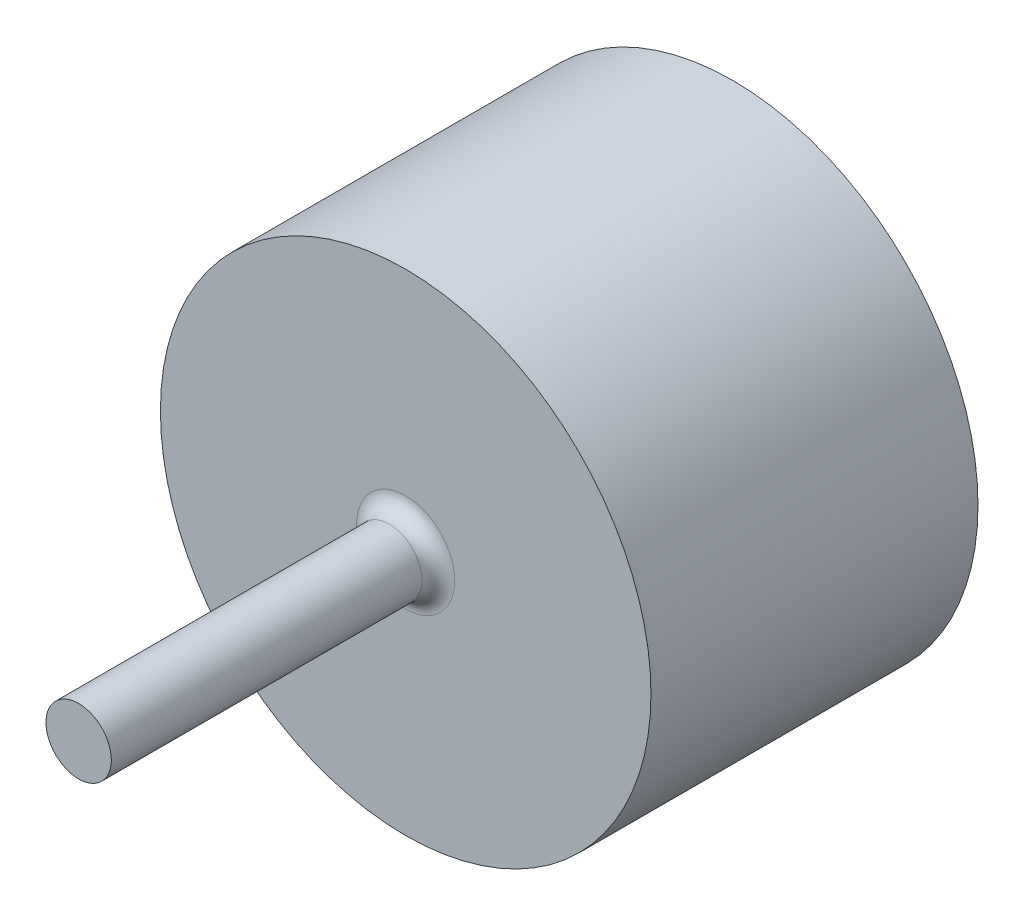
SolidWorks part; units mm, degrees
ref_plane "前视基准面" through (0, 0, 0) normal (0, 0, 1) x (1, 0, 0)
ref_plane "上视基准面" through (0, 0, 0) normal (0, 1, 0) x (1, 0, 0)
ref_plane "右视基准面" through (0, 0, 0) normal (1, 0, 0) x (0, 0, -1)
sketch "草图1" plane through (0, 0, 0) normal (0, 0, 1) x (1, 0, 0)
  circle A0 centre (0, 0) radius 75
  dimension "D1" = 150
extrude "凸台-拉伸1" add sketch "草图1" along normal blind 100
sketch "草图2" plane through (0, 0, 100) normal (0, 0, 1) x (1, 0, 0)
  circle A0 centre (0, 0) radius 10
  dimension "D1" = 20
extrude "凸台-拉伸2" add sketch "草图2" along normal blind 100
fillet "圆角1" radius 5 1 edges at (10, 0, 100)
